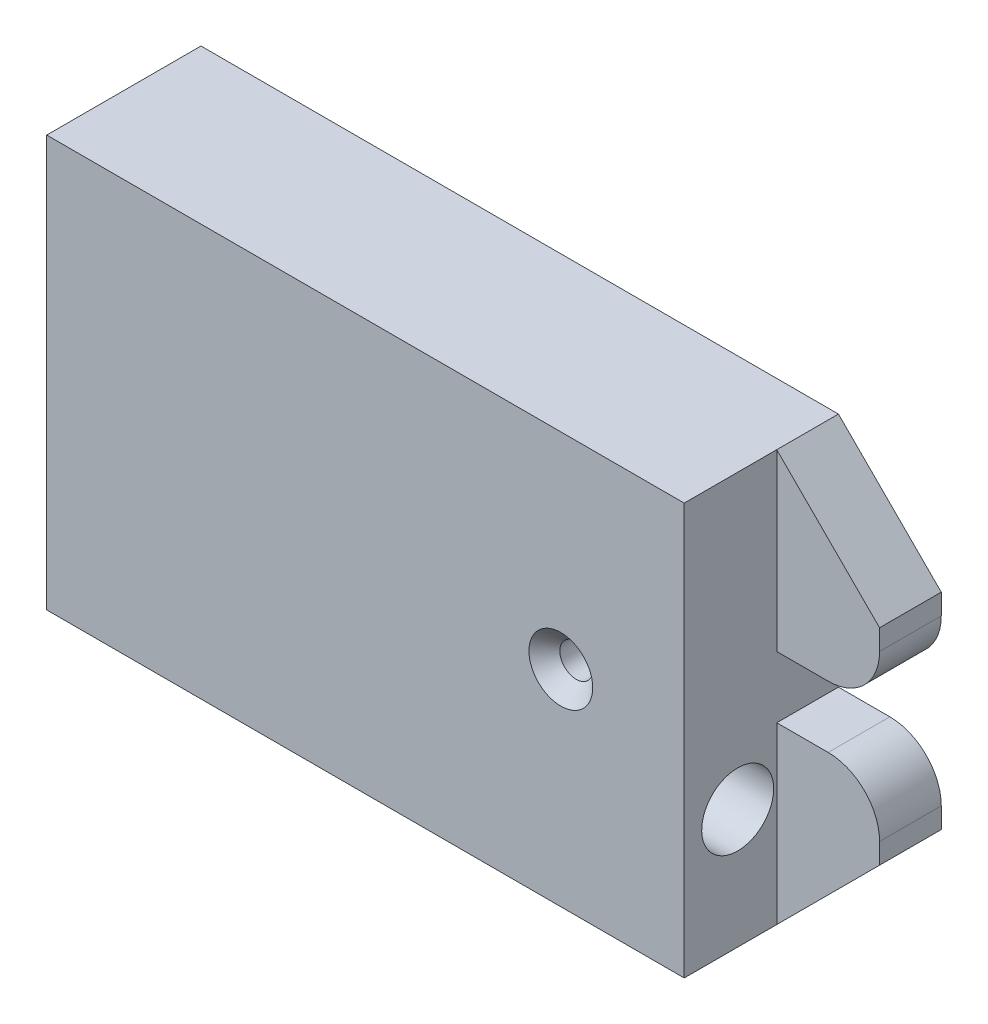
SolidWorks part; units mm, degrees
ref_plane "Plan de face" through (0, 0, 0) normal (0, 0, 1) x (1, 0, 0)
ref_plane "Plan de dessus" through (0, 0, 0) normal (0, 1, 0) x (1, 0, 0)
ref_plane "Plan de droite" through (0, 0, 0) normal (1, 0, 0) x (0, 0, -1)
sketch "Esquisse1" plane through (0, 0, 0) normal (0, 0, 1) x (1, 0, 0)
  line L0 (0, 20) -> (0, 0) construction
  line L1 (-31, 20) -> (31, 20)
  line L2 (-31, 20) -> (-31, -20)
  line L3 (-31, -20) -> (31, -20)
  line L4 (31, 20) -> (31, -20)
  line L5 (0, 0) -> (-31, 0) construction
  line L6 (0, 0) -> (19, 0) construction
  circle A0 centre (19, 0) radius 1.6
  dimension "D3" = 3.2
  dimension "D4" = 50
  dimension "D1" = 62
  dimension "D2" = 40
extrude "Extrusion1" add sketch "Esquisse1" along normal blind 15
sketch "Esquisse2" plane through (0, 0, 0) normal (0, 0, -1) x (-1, 0, 0)
  line L0 (-31, 20) -> (-41, 10)
  line L1 (-41, 10) -> (-41, 3)
  line L2 (-41, 3) -> (-31, 3)
  line L3 (-31, -20) -> (-31, 20) construction
  line L4 (-31, -3) -> (-41, -3)
  line L5 (-41, -3) -> (-41, -10)
  line L6 (-41, -10) -> (-31, -20)
  line M3 (-31, 20) -> (-31, -20)
  dimension "D1" = 10
  dimension "D2" = 10
  dimension "D3" = 6
extrude "Extrusion2" add sketch "Esquisse2" against normal blind 6 contours L1 L2 L0 M3 | L5 L6 L4 M3
fillet "Congé1" radius 5 2 edges at (41, -3, 3) (41, 3, 3)
chamfer "Chanfrein1" distance 1.5 angle 45 1 edges at (20.6, 0, 15)
sketch "Esquisse3" plane through (-31, 0, 0) normal (-1, 0, 0) x (0, 0, 1)
  line L0 (0, 20) -> (0, -20) construction
  line L1 (15, -20) -> (0, -20) construction
  circle A0 centre (9.8, -8.8) radius 3.1
  dimension "D1" = 9.8
  dimension "D2" = 11.2
  dimension "D3" = 6.2
extrude "Enlèv. mat.-Extru.1" cut sketch "Esquisse3" against normal through all
sketch "Esquisse4" plane through (31, 0, 0) normal (1, 0, 0) x (0, 0, -1)
  line L0 (-9.8, -8.8) -> (-9.8, -8.4) construction
  circle A0 centre (-9.8, -8.4) radius 3.5
  circle A1 centre (-9.8, -8.8) radius 3.1 construction
  dimension "D1" = 7
extrude "Enlèv. mat.-Extru.2" cut sketch "Esquisse4" against normal blind 10
hole_wizard "Trou taraudé M5x0.81" positions "Esquisse3D1" profile "Esquisse5" tap size "M5x0.8" standard "ISO"
sketch3d "Esquisse3D1"
  line L0 (-31, 20, 15) -> (-31, -20, 15) construction
  line L1 (-31, -20, 15) -> (-31, -20, 0) construction
  point P0 (-31, 6.2, 7.5)
  dimension "D1" = 7.5
  dimension "D2" = 26.2
sketch "Esquisse5" plane through (-31, 6.2, 7.5) normal (0, 1, 0) x (0, 0, 1)
  line L0 (0, 0) -> (0, 23.2618)
  line L1 (0, 23.2618) -> (2.1, 22)
  line L2 (2.1, 22) -> (2.1, 0)
  line L5 (2.1, 0) -> (0, 0)
  line L10 (0, 23.2618) -> (-2.1, 22) construction
  line L11 (0, -6.35) -> (0, 107.95) construction
  dimension "Diamètre du trou pour taraudage" = 4.2
  dimension "Profondeur du trou pour taraudage" = 22
  dimension "Angle de pointe" = 118
cosmetic thread "Filetage de perçage1" parameters "D1"=20, "D2"=5
